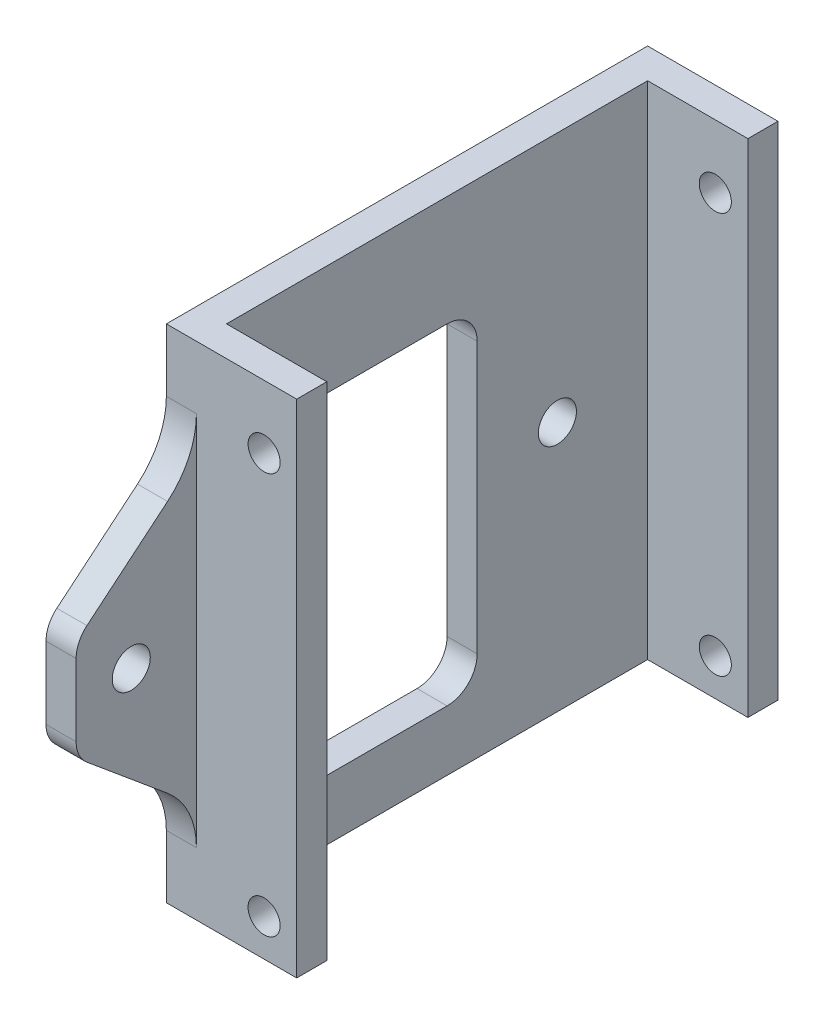
SolidWorks part; units mm, degrees
ref_plane "Front Plane" through (0, 0, 0) normal (0, 0, 1) x (1, 0, 0)
ref_plane "Top Plane" through (0, 0, 0) normal (0, 1, 0) x (1, 0, 0)
ref_plane "Right Plane" through (0, 0, 0) normal (1, 0, 0) x (0, 0, -1)
sketch "Sketch1" plane through (0, 0, 0) normal (0, 1, 0) x (1, 0, 0)
  line L0 (0, 0) -> (0, 48)
  line L1 (0, 48) -> (3, 48)
  line L3 (3, 3) -> (13, 3)
  line L4 (13, 3) -> (13, 0)
  line L9 (3, 48) -> (13, 48)
  line L10 (13, 48) -> (13, 45)
  line L11 (13, 45) -> (3, 45)
  line L12 (3, 45) -> (3, 3)
  line L14 (0, 0) -> (0, -12)
  line L15 (0, -12) -> (3, -12)
  line L16 (3, -12) -> (3, 0)
  line L17 (3, 0) -> (13, 0)
  dimension "D1" = 3
  dimension "D2" = 45
  dimension "D3" = 60
  dimension "D4" = 10
extrude "Boss-Extrude1" add sketch "Sketch1" along normal blind 50
sketch "Sketch3" plane through (0, 0, 0) normal (0, 0, 1) x (1, 0, 0)
  circle A0 centre (9.75, 43.7) radius 1.6
  circle A1 centre (9.75, 3.7) radius 1.6
  point P0 (9.75, 3.7)
  point P1 (9.75, 43.7)
  dimension "D1" = 3.2
extrude "Cut-Extrude1" cut sketch "Sketch3" against normal through all
sketch "Sketch4" plane through (3, 0, 0) normal (1, 0, 0) x (0, 0, -1)
  line L0 (-12, 25) -> (0, 25) construction
  line L1 (-12, 50) -> (-12, 0) construction
  line L2 (0, 50) -> (0, 0) construction
  line L4 (0, 50) -> (-12, 50)
  line L5 (-12, 50) -> (-12, 30)
  line L6 (0, 50) -> (0, 43.747)
  line L7 (-2.8785, 37.6012) -> (-12, 30)
  line L8 (0, 0) -> (0, 6.253)
  line L9 (0, 0) -> (-12, 0)
  line L10 (-12, 0) -> (-12, 20)
  line L11 (-2.8785, 12.3988) -> (-12, 20)
  line L12 (4.6, 4.1) -> (4.6, 0.1) construction
  line L13 (28, 39) -> (4.6, 39)
  line L14 (28, 39) -> (28, 6)
  line L15 (28, 6) -> (4.6, 6)
  line L16 (4.6, 39) -> (4.6, 6)
  line L17 (3, 0) -> (45, 0) construction
  line L18 (3, 50) -> (45, 50) construction
  line L19 (3, 50) -> (3, 0) construction
  arc A0 (0, 6.253) -> (-2.8785, 12.3988) centre (-8, 6.253) ccw
  arc A1 (0, 43.747) -> (-2.8785, 37.6012) centre (-8, 43.747) cw
  point P32 (0, 10)
  point P35 (0, 40)
  dimension "D6" = 8
  dimension "D1" = 10
  dimension "D2" = 10
  dimension "D3" = 6
  dimension "D4" = 11
  dimension "D5" = 25
extrude "Cut-Extrude2" cut sketch "Sketch4" against normal through all contours L7 L5 L4 L6 A1 | L8 A0 L11 L10 L9 | L14 L13 L16 L15
fillet "Fillet1" radius 3 2 edges at (1.5, 20, 12) (1.5, 30, 12)
fillet "Fillet2" radius 3 4 edges at (1.5, 6, -4.6) (1.5, 6, -28) (1.5, 39, -4.6) (1.5, 39, -28)
sketch "Sketch5" plane through (3, 0, 0) normal (1, 0, 0) x (0, 0, -1)
  line L0 (-12, 25) -> (48, 25) construction
  line L1 (-12, 28.5949) -> (-12, 21.4051) construction
  line L2 (48, 50) -> (48, 0) construction
  line L3 (45, 50) -> (45, 0) construction
  point P6 (-6.5, 25)
  point P7 (36, 25)
  dimension "D1" = 9
  dimension "D2" = 5.5
hole_wizard "#6 Clearance Hole1" positions "Sketch6" profile "Sketch8" hole size "#6" standard "ANSI Inch" end condition through all
sketch "Sketch6" plane through (3, 0, 0) normal (1, 0, 0) x (0, 0, -1)
  point P0 (-6.5, 25)
  point P3 (36, 25)
sketch "Sketch8" plane through (3, 25, 6.5) normal (0, 1, 0) x (0, 0, -1)
  line L0 (0, 0) -> (0, 3)
  line L1 (0, 3) -> (1.8986, 3)
  line L2 (1.8986, 3) -> (1.8986, 0)
  line L5 (1.8986, 0) -> (0, 0)
  line L11 (0, -6.35) -> (0, 107.95) construction
  dimension "Thru Hole Dia." = 3.7973
  dimension "Thru Hole Depth" = 3
